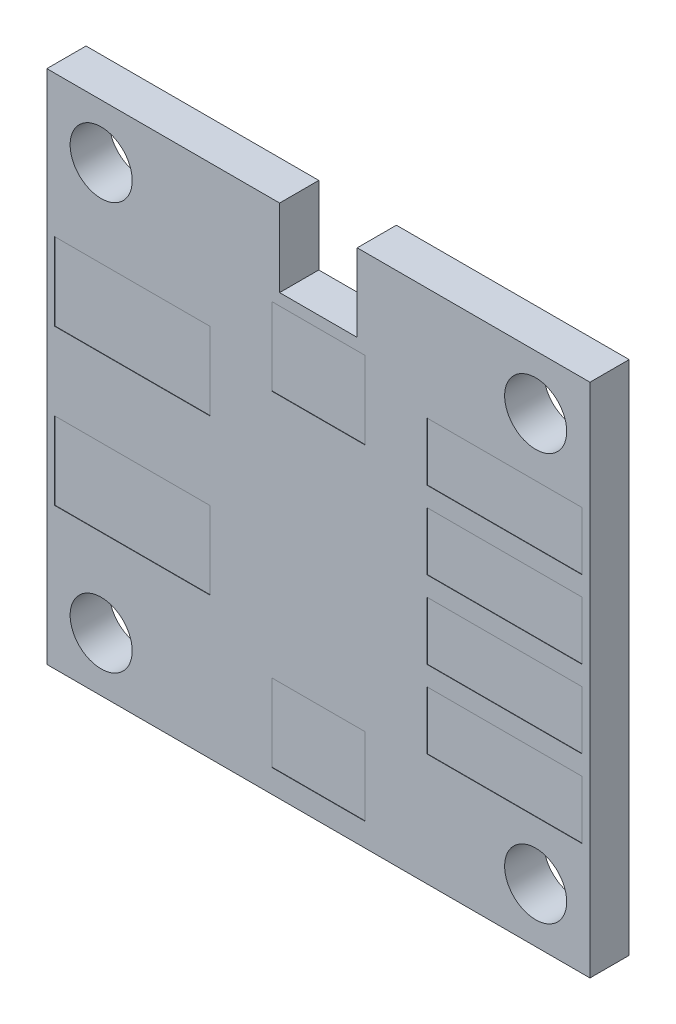
SolidWorks part; units mm, degrees
ref_plane "Front" through (0, 0, 0) normal (0, 0, 1) x (1, 0, 0)
ref_plane "Top" through (0, 0, 0) normal (0, 1, 0) x (1, 0, 0)
ref_plane "Right" through (0, 0, 0) normal (1, 0, 0) x (0, 0, -1)
sketch "草图1" plane through (0, 0, 0) normal (0, 0, 1) x (1, 0, 0)
  line L1 (0, 0) -> (14, 0)
  line L2 (0, 0) -> (0, 13.3)
  line L3 (0, 13.3) -> (14, 13.3)
  line L4 (14, 0) -> (14, 13.3)
  line L5 (6, 13.3) -> (8, 13.3)
  line L6 (6, 13.3) -> (6, 11.3)
  line L7 (6, 11.3) -> (8, 11.3)
  line L8 (8, 13.3) -> (8, 11.3)
  circle A0 centre (1.4, 11.9) radius 0.8
  circle A1 centre (1.4, 1.4) radius 0.8
  circle A2 centre (12.6, 11.9) radius 0.8
  circle A3 centre (12.6, 1.4) radius 0.8
  dimension "D3" = 1.6
  dimension "D4" = 1.6
  dimension "D5" = 1.6
  dimension "D6" = 1.6
  dimension "D1" = 14
  dimension "D2" = 13.3
  dimension "D7" = 1.4
  dimension "D8" = 1.4
  dimension "D9" = 1.4
  dimension "D10" = 1.4
  dimension "D11" = 1.4
  dimension "D12" = 1.4
  dimension "D13" = 1.4
  dimension "D14" = 1.4
  dimension "D20" = 2
  dimension "D22" = 2
extrude "凸台-拉伸2" add sketch "草图1" along normal blind 1
sketch "草图2" plane through (0, 0, 1) normal (0, 0, 1) x (1, 0, 0)
  line L0 (0, 0) -> (0, 13.3) construction
  line L1 (0.2, 9.65) -> (4.2, 9.65)
  line L2 (0.2, 9.65) -> (0.2, 7.65)
  line L3 (0.2, 7.65) -> (4.2, 7.65)
  line L4 (4.2, 9.65) -> (4.2, 7.65)
  line L5 (0.2, 5.65) -> (4.2, 5.65)
  line L6 (0.2, 5.65) -> (0.2, 3.65)
  line L7 (0.2, 3.65) -> (4.2, 3.65)
  line L8 (4.2, 5.65) -> (4.2, 3.65)
  line L9 (14, 0) -> (14, 13.3) construction
  line L10 (13.8, 10.4) -> (9.8, 10.4)
  line L11 (13.8, 10.4) -> (13.8, 8.9)
  line L12 (13.8, 8.9) -> (9.8, 8.9)
  line L13 (9.8, 10.4) -> (9.8, 8.9)
  line L14 (13.8, 8.4) -> (9.8, 8.4)
  line L15 (13.8, 8.4) -> (13.8, 6.9)
  line L16 (13.8, 6.9) -> (9.8, 6.9)
  line L17 (9.8, 8.4) -> (9.8, 6.9)
  line L18 (13.8, 6.4) -> (9.8, 6.4)
  line L19 (13.8, 6.4) -> (13.8, 4.9)
  line L20 (13.8, 4.9) -> (9.8, 4.9)
  line L21 (9.8, 6.4) -> (9.8, 4.9)
  line L22 (13.8, 4.4) -> (9.8, 4.4)
  line L23 (13.8, 4.4) -> (13.8, 2.9)
  line L24 (13.8, 2.9) -> (9.8, 2.9)
  line L25 (9.8, 4.4) -> (9.8, 2.9)
  line L26 (6, 11.3) -> (8, 11.3) construction
  line L28 (8, 13.3) -> (14, 13.3) construction
  line L29 (5.8, 2.6) -> (8.2, 2.6)
  line L30 (5.8, 2.6) -> (5.8, 0.6)
  line L31 (5.8, 0.6) -> (8.2, 0.6)
  line L32 (8.2, 2.6) -> (8.2, 0.6)
  line L33 (5.8, 11) -> (8.2, 11)
  line L34 (5.8, 11) -> (5.8, 9)
  line L35 (5.8, 9) -> (8.2, 9)
  line L36 (8.2, 11) -> (8.2, 9)
  line L37 (0, 0) -> (14, 0) construction
  point P10 (0, 6.65)
  point P29 (14, 6.65)
  point P36 (7, 11.3)
  point P45 (7, 11)
  dimension "D25" = 2
  dimension "D26" = 2.4
  dimension "D1" = 2
  dimension "D2" = 2
  dimension "D3" = 4
  dimension "D4" = 4
  dimension "D5" = 0.2
  dimension "D6" = 0.2
  dimension "D7" = 1
  dimension "D8" = 1
  dimension "D9" = 1.5
  dimension "D10" = 4
  dimension "D11" = 4
  dimension "D12" = 4
  dimension "D13" = 4
  dimension "D14" = 1.5
  dimension "D15" = 1.5
  dimension "D16" = 1.5
  dimension "D17" = 0.2
  dimension "D18" = 0.2
  dimension "D19" = 0.2
  dimension "D20" = 0.2
  dimension "D21" = 0.5
  dimension "D22" = 0.5
  dimension "D23" = 0.5
  dimension "D24" = 0.25
  dimension "D28" = 0.6
  dimension "D29" = 2
  dimension "D30" = 2.4
  dimension "D31" = 0
  dimension "D32" = 2.3
extrude "凸台-拉伸3" add sketch "草图2" along normal blind 0.01
